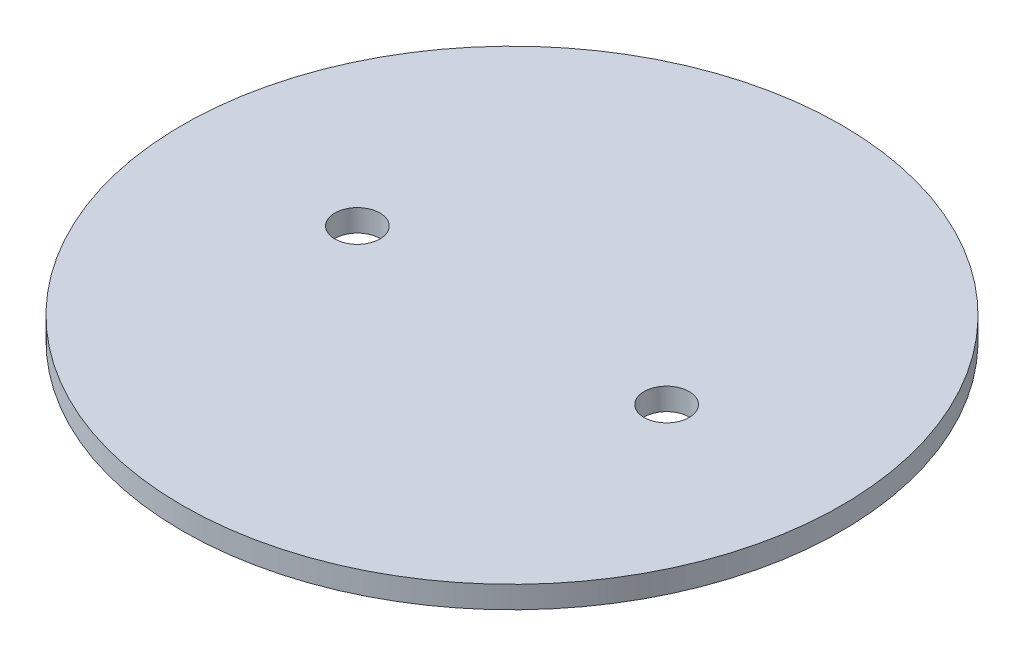
SolidWorks part; units mm, degrees
ref_plane "Front Plane" through (0, 0, 0) normal (0, 0, 1) x (1, 0, 0)
ref_plane "Top Plane" through (0, 0, 0) normal (0, 1, 0) x (1, 0, 0)
ref_plane "Right Plane" through (0, 0, 0) normal (1, 0, 0) x (0, 0, -1)
sketch "Sketch1" plane through (0, 0, 0) normal (0, 1, 0) x (1, 0, 0)
  line L0 (-22.225, 0) -> (22.225, 0) construction
  circle A0 centre (0, 0) radius 47.371
  circle A1 centre (22.225, 0) radius 3.2385
  circle A2 centre (-22.225, 0) radius 3.2385
  point P6 (0, 0)
  point P11 (0, 0)
  dimension "D1" = 6.477
  dimension "D2" = 94.742
  dimension "D3" = 44.45
extrude "Boss-Extrude1" add sketch "Sketch1" along normal blind 3.175
